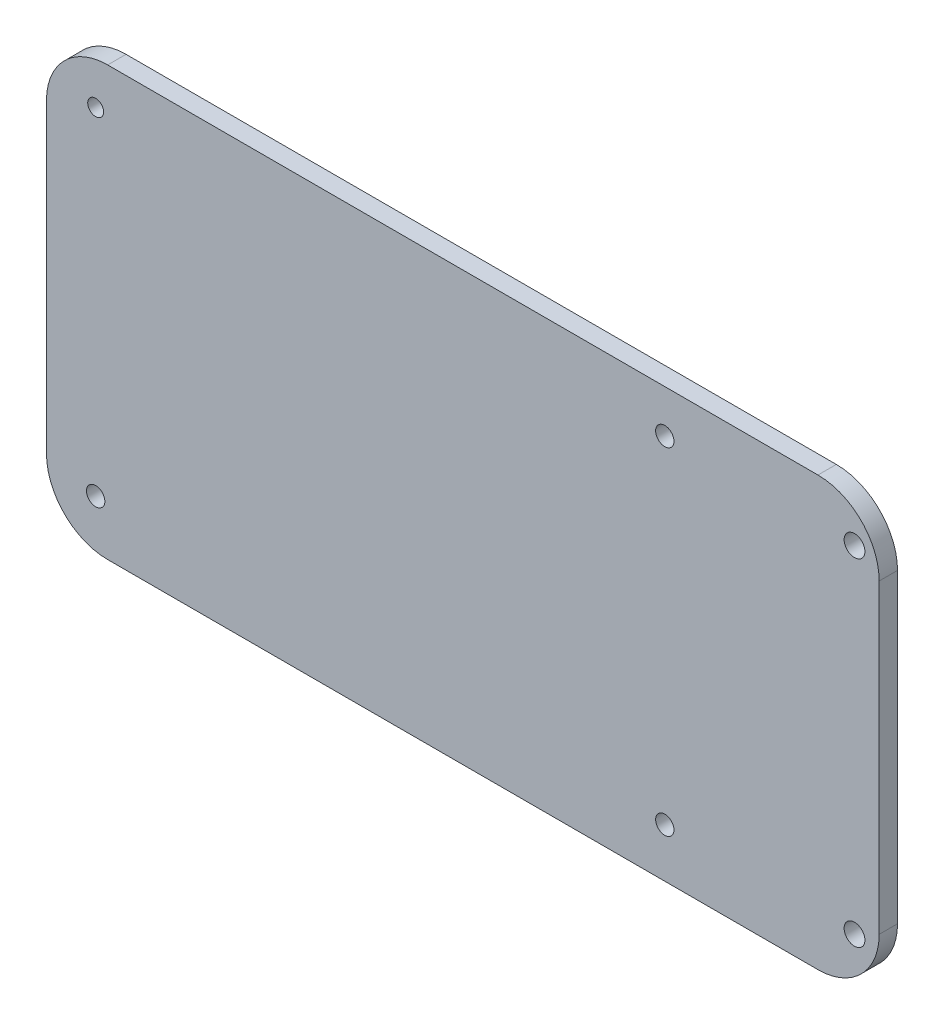
SolidWorks part; units mm, degrees
ref_plane "Front Plane" through (0, 0, 0) normal (0, 0, 1) x (1, 0, 0)
ref_plane "Top Plane" through (0, 0, 0) normal (0, 1, 0) x (1, 0, 0)
ref_plane "Right Plane" through (0, 0, 0) normal (1, 0, 0) x (0, 0, -1)
sketch "Sketch1" plane through (0, 0, 0) normal (0, 0, 1) x (1, 0, 0)
  line L0 (-66.9683, 11.979) -> (-66.9683, -38.021)
  line L1 (-56.9683, -48.021) -> (59.0949, -48.021)
  line L2 (69.0949, 11.979) -> (69.0949, -38.021)
  line L3 (59.0949, 21.979) -> (-56.9683, 21.979)
  arc A0 (69.0949, 11.979) -> (59.0949, 21.979) centre (59.0949, 11.979) ccw
  circle A1 centre (-58.9317, 14.979) radius 1.3
  circle A2 centre (34.0683, 14.979) radius 1.5
  circle A3 centre (34.0683, -40.021) radius 1.5
  circle A4 centre (-58.9317, -40.021) radius 1.5
  arc A5 (-66.9683, 11.979) -> (-56.9683, 21.979) centre (-56.9683, 11.979) cw
  arc A8 (59.0949, -48.021) -> (69.0949, -38.021) centre (59.0949, -38.021) ccw
  arc A11 (-66.9683, -38.021) -> (-56.9683, -48.021) centre (-56.9683, -38.021) ccw
  dimension "D1" = 10
extrude "Boss-Extrude1" add sketch "Sketch1" along normal blind 3
hole_wizard "M3 Clearance Hole1" positions "Sketch3" profile "Sketch2" hole size "M3" standard "ISO" end condition through all
sketch "Sketch3" plane through (0, 0, 0) normal (0, 0, -1) x (-1, 0, 0)
  point P0 (-65.0658, -40.021)
  point P2 (-65.0658, 14.979)
sketch "Sketch2" plane through (65.0658, -40.021, 0) normal (1, 0, 0) x (0, 1, 0)
  line L0 (0, 0) -> (0, 3)
  line L1 (0, 3) -> (1.7, 3)
  line L2 (1.7, 3) -> (1.7, 0)
  line L5 (1.7, 0) -> (0, 0)
  line L11 (0, -6.35) -> (0, 107.95) construction
  dimension "Thru Hole Dia." = 3.4
  dimension "Thru Hole Depth" = 3
